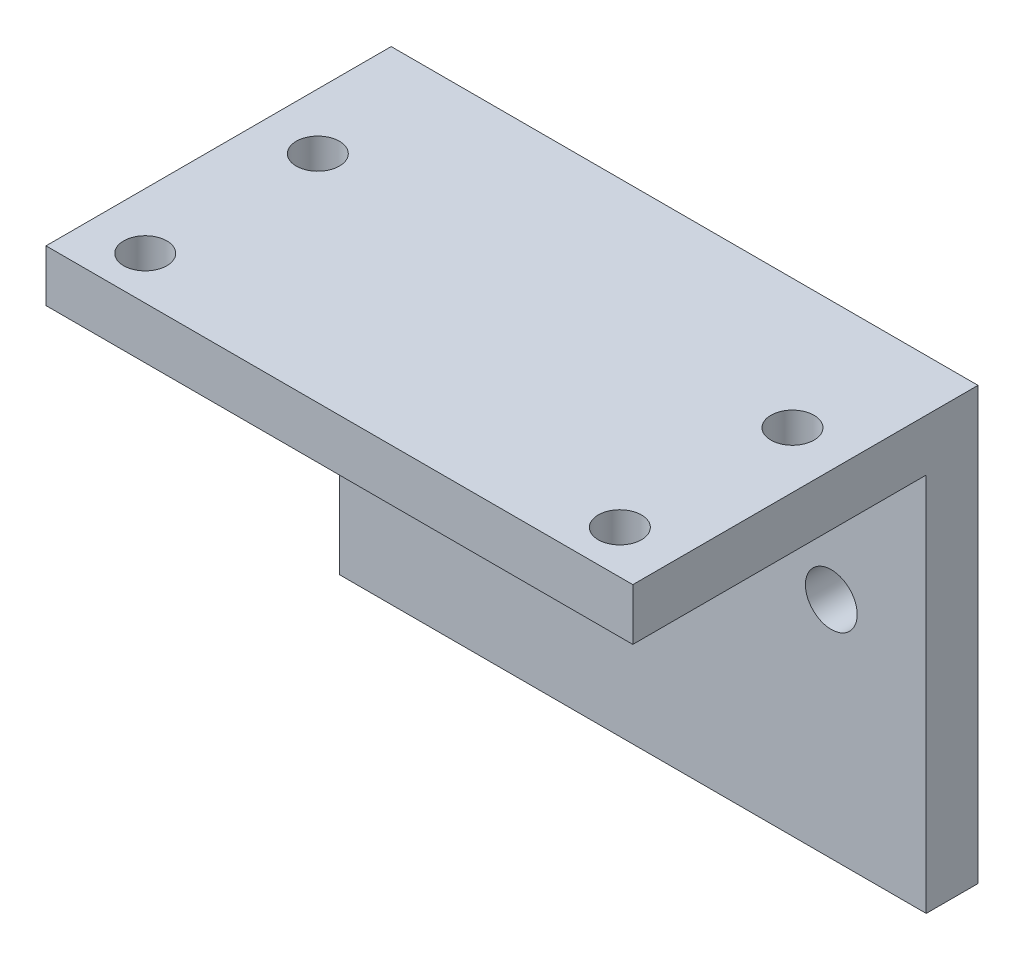
SolidWorks part; units mm, degrees
material "6061 合金"
ref_plane "前视基准面" through (0, 0, 0) normal (0, 0, 1) x (1, 0, 0)
ref_plane "上视基准面" through (0, 0, 0) normal (0, 1, 0) x (1, 0, 0)
ref_plane "右视基准面" through (0, 0, 0) normal (1, 0, 0) x (0, 0, -1)
sketch "草图1" plane through (0, 0, 0) normal (0, 1, 0) x (1, 0, 0)
  line L0 (0, 0) -> (0, 40) construction
  line L1 (-34, 40) -> (34, 40)
  line L2 (-34, 40) -> (-34, 0)
  line L3 (-34, 0) -> (34, 0)
  line L4 (34, 40) -> (34, 0)
  line L5 (0, 0) -> (51.5608, 0) construction
  line L6 (-27.5, 25) -> (27.5, 25) construction
  line L7 (-27.5, 25) -> (-27.5, 5) construction
  line L8 (27.5, 25) -> (27.5, 5) construction
  line L9 (-27.5, 5) -> (27.5, 5) construction
  line L10 (-27.5, 25) -> (27.5, 5) construction
  line L11 (27.5, 25) -> (-27.5, 5) construction
  circle A0 centre (-27.5, 25) radius 2.5
  circle A1 centre (27.5, 25) radius 2.5
  circle A2 centre (-27.5, 5) radius 2.5
  circle A3 centre (27.5, 5) radius 2.5
  point P9 (0, 15)
  dimension "D7" = 5
  dimension "D8" = 5
  dimension "D9" = 5
  dimension "D10" = 5
  dimension "D1" = 68
  dimension "D2" = 40
  dimension "D3" = 55
  dimension "D4" = 20
  dimension "D5" = 15
extrude "凸台-拉伸1" add sketch "草图1" along normal blind 6
sketch "草图3" plane through (0, 6, 0) normal (0, 1, 0) x (1, 0, 0)
  line L0 (34, 40) -> (-34, 40) construction
  line L1 (-34, 40) -> (34, 40)
  line L2 (-34, 40) -> (-34, 34)
  line L3 (-34, 34) -> (34, 34)
  line L4 (34, 40) -> (34, 34)
  line L5 (-34, 40) -> (-34, 0) construction
  point P8 (-40.124, -0.0172)
  point P11 (96.2303, 89.4598)
  dimension "D2" = 68
  dimension "D3" = 6
extrude "凸台-拉伸2" add sketch "草图3" against normal blind 50
sketch "草图4" plane through (0, 0, -34) normal (0, 0, 1) x (1, 0, 0)
  line L0 (-1, -45) -> (-1, 0) construction
  line L2 (-1, -18) -> (23, -18) construction
  line L3 (34, 6) -> (-34, 6) construction
  line L4 (34, -44) -> (34, 0) construction
  circle A0 centre (-1, -18) radius 8
  circle A1 centre (23, -18) radius 3
  circle A2 centre (-25, -18) radius 3
  dimension "D1" = 16
  dimension "D3" = 6
  dimension "D2" = 24
  dimension "D4" = 24
  dimension "D5" = 35
extrude "切除-拉伸1" cut sketch "草图4" against normal up to next
